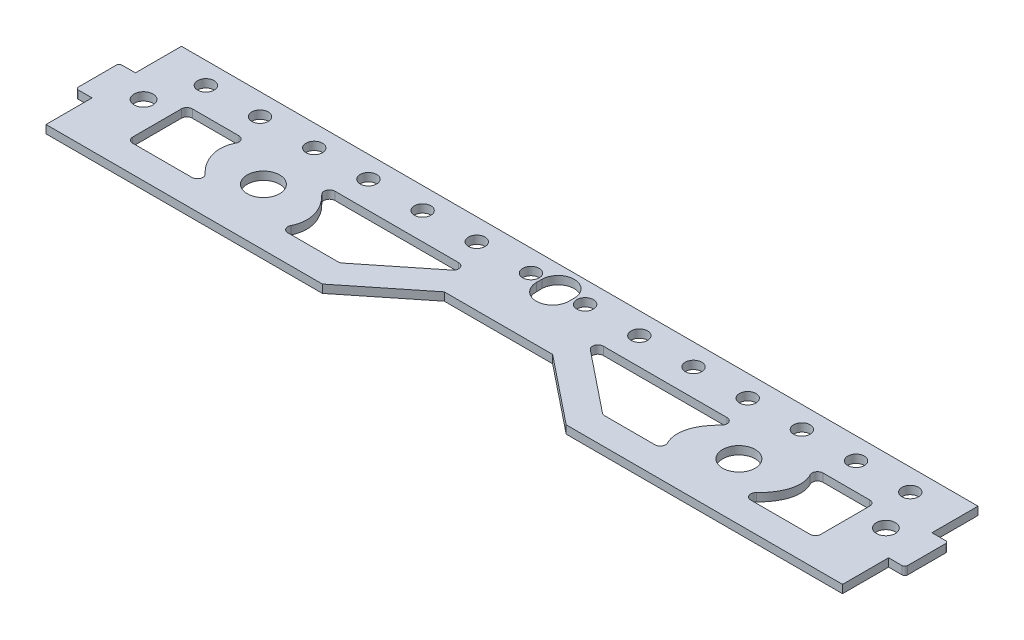
SolidWorks part; units mm, degrees
material "Thornel Mat VMA"
ref_plane "前视基准面" through (0, 0, 0) normal (0, 0, 1) x (1, 0, 0)
ref_plane "上视基准面" through (0, 0, 0) normal (0, 1, 0) x (1, 0, 0)
ref_plane "右视基准面" through (0, 0, 0) normal (1, 0, 0) x (0, 0, -1)
sketch "草图1" plane through (0, 0, 0) normal (0, 1, 0) x (1, 0, 0)
  line L1 (-73.5, 12.5) -> (73.5, 12.5)
  line L2 (-73.5, 12.5) -> (-73.5, -12.5)
  line L3 (-73.5, -12.5) -> (73.5, -12.5)
  line L4 (73.5, 12.5) -> (73.5, -12.5)
  line L5 (-73.5, 12.5) -> (73.5, -12.5) construction
  line L6 (-73.5, -12.5) -> (73.5, 12.5) construction
  point P0 (0, 0)
  dimension "D1" = 147
  dimension "D2" = 25
extrude "凸台-拉伸1" add sketch "草图1" along normal blind 1.5
sketch "草图2" plane through (0, 0, 0) normal (0, -1, 0) x (1, 0, 0)
  line L0 (10, 2.5) -> (-10, 2.5)
  line L1 (-10, 2.5) -> (-22.5, 12.5)
  line L2 (-73.5, 12.5) -> (73.5, 12.5) construction
  line L3 (-22.5, 12.5) -> (22.5, 12.5)
  line L4 (22.5, 12.5) -> (10, 2.5)
  point P5 (0, 2.5)
  point P7 (0, 12.5)
  dimension "D1" = 10
  dimension "D2" = 20
  dimension "D3" = 45
extrude "切除-拉伸1" cut sketch "草图2" against normal through all
sketch "草图4" plane through (0, 1.5, 0) normal (0, 1, 0) x (1, 0, 0)
  line L0 (73, 12.5) -> (-73, 12.5) construction
  line L1 (73.5, -12.5) -> (63.5, -12.5)
  line L2 (73.5, -12.5) -> (73.5, 12.5)
  line L3 (73.5, 12.5) -> (63.5, 12.5)
  line L4 (63.5, -12.5) -> (63.5, 12.5)
  line L5 (73.5, -12) -> (73.5, 12) construction
  dimension "D1" = 10
  dimension "D2" = 25
extrude "凸台-拉伸2" add sketch "草图4" against normal up to surface (1.5 mm away) up to face at (0, 0, 3.75)
mirror "镜向4" about plane through (0, 0, 0) normal (1, 0, 0) of "凸台-拉伸2"
sketch "草图5" plane through (0, 0, 0) normal (0, -1, 0) x (1, 0, 0)
  line L0 (73.5, -12.5) -> (-73.5, -12.5) construction
  line L1 (-73.5, -12.5) -> (-73.5, 12.5) construction
  line L2 (73.5, 12.5) -> (73.5, -12.5) construction
  circle A0 centre (-68.5, -0.5) radius 1.75
  circle A1 centre (68.5, -0.5) radius 1.75
  dimension "D2" = 5
  dimension "D4" = 5
  dimension "D5" = 3.5
  dimension "D1" = 12
  dimension "D3" = 12
extrude "切除-拉伸3" cut sketch "草图5" against normal through all
sketch "草图6" plane through (0, 1.5, 0) normal (0, 1, 0) x (1, 0, 0)
  line L0 (0, 8.5) -> (0, 7.5) construction
  line L1 (3, 8.5) -> (3, 7.5)
  line L2 (-3, 8.5) -> (-3, 7.5)
  arc A0 (3, 8.5) -> (-3, 8.5) centre (0, 8.5) ccw
  arc A1 (-3, 7.5) -> (3, 7.5) centre (0, 7.5) ccw
  point P3 (0, 8)
  dimension "D3" = 3
  dimension "D1" = 8
  dimension "D2" = 1
extrude "切除-拉伸4" cut sketch "草图6" against normal through all
sketch "草图7" plane through (0, 1.5, 0) normal (0, 1, 0) x (1, 0, 0)
  line L0 (-68.5, 0) -> (68.5, 0) construction
  line L1 (-73.5, 12.5) -> (-73.5, -12.5) construction
  line L2 (-76.5, -4) -> (-73.5, -4)
  line L3 (-76.5, -4) -> (-76.5, 4)
  line L4 (-76.5, 4) -> (-73.5, 4)
  line L5 (-73.5, -4) -> (-73.5, 4)
  line L6 (-76.5, -4) -> (-73.5, 4) construction
  line L7 (-76.5, 4) -> (-73.5, -4) construction
  line L8 (73.5, -12.5) -> (73.5, 12.5) construction
  line L9 (76.5, -4) -> (73.5, -4)
  line L10 (76.5, -4) -> (76.5, 4)
  line L11 (76.5, 4) -> (73.5, 4)
  line L12 (73.5, -4) -> (73.5, 4)
  line L13 (76.5, -4) -> (73.5, 4) construction
  line L14 (76.5, 4) -> (73.5, -4) construction
  point P1 (-75, 0)
  point P12 (75, 0)
  dimension "D1" = 8
  dimension "D2" = 3
extrude "凸台-拉伸3" add sketch "草图7" against normal up to surface (1.5 mm away) up to face at (0, 0, -8)
fillet "圆角4" radius 0.5 4 edges at (76.5, 0.75, 4) (76.5, 0.75, -4) (-76.5, 0.75, 4) (-76.5, 0.75, -4)
sketch "草图8" plane through (0, 0, 0) normal (0, -1, 0) x (1, 0, 0)
  line L0 (-65, -8.5) -> (-45, -8.5) construction
  line L2 (73.5, -12.5) -> (-73.5, -12.5) construction
  line L3 (0, 0) -> (0, -50000) construction
  circle A0 centre (-65, -8.5) radius 1.525
  circle A1 centre (-45, -8.5) radius 1.525
  circle A2 centre (-35, -8.5) radius 1.525
  circle A3 centre (-55, -8.5) radius 1.525
  circle A4 centre (-25, -8.5) radius 1.525
  circle A5 centre (-45, -8.5) radius 1.525
  circle A6 centre (-15, -8.5) radius 1.525
  circle A7 centre (-35, -8.5) radius 1.525
  circle A8 centre (-5, -8.5) radius 1.525
  circle A9 centre (-25, -8.5) radius 1.525
  circle A10 centre (5, -8.5) radius 1.525
  circle A11 centre (-15, -8.5) radius 1.525
  circle A12 centre (15, -8.5) radius 1.525
  circle A13 centre (-5, -8.5) radius 1.525
  circle A14 centre (25, -8.5) radius 1.525
  circle A15 centre (5, -8.5) radius 1.525
  circle A16 centre (35, -8.5) radius 1.525
  circle A17 centre (15, -8.5) radius 1.525
  circle A18 centre (45, -8.5) radius 1.525
  circle A19 centre (25, -8.5) radius 1.525
  circle A20 centre (55, -8.5) radius 1.525
  circle A21 centre (35, -8.5) radius 1.525
  circle A22 centre (65, -8.5) radius 1.525
  circle A23 centre (45, -8.5) radius 1.525
  dimension "D2" = 3.05
  dimension "D6" = 10
  dimension "D1" = 20
  dimension "D4" = 4
  dimension "D5" = 12
extrude "切除-拉伸5" cut sketch "草图8" against normal blind 10 contours A14 | A22 | A16 | A18 | A12 | A10 | A8 | A6 | A4 | A2 | A1 | A3 | A20 | A0
sketch "草图9" plane through (0, 0, 0) normal (0, -1, 0) x (1, 0, 0)
  line L0 (-63.5, 7.5) -> (-24.2539, 7.5)
  line L1 (-24.2539, 7.5) -> (-10.5039, -3.5)
  line L2 (-10.5039, -3.5) -> (-63.5, -3.5)
  line L3 (-63.5, -3.5) -> (-63.5, 7.5)
  line L4 (0, 0) -> (0, -50000) construction
  line L5 (-22.5, 12.5) -> (-10, 2.5) construction
  line L6 (-73.5, 12.5) -> (-22.5, 12.5) construction
  line L7 (-73.5, 4) -> (-73.5, 12.5) construction
  line L8 (-43.877, 2) -> (-43.877, 7.5) construction
  line L9 (-43.877, 2) -> (-63.5, 2) construction
  line L10 (-53.2739, -1.4202) -> (-43.877, 2) construction
  circle A0 centre (-55, -8.5) radius 1.525 construction
  circle A1 centre (-43.877, 2) radius 3
  ellipse E0 centre (-43.877, 2) end of major axis (-34.48, 5.4202) minor radius 7
  dimension "D5" = 7
  dimension "D6" = 6
  dimension "D1" = 10
  dimension "D2" = 5
  dimension "D3" = 5
  dimension "D4" = 5
  dimension "D7" = 10
  dimension "D8" = 160
extrude "切除-拉伸6" cut sketch "草图9" against normal blind 10
mirror "镜向5" about plane through (0, 0, 0) normal (1, 0, 0) of "切除-拉伸6"
fillet "圆角5" radius 1 16 edges at (39.1858, 0.75, -3.5) (51.8484, 0.75, -3.5) (10.5039, 0.75, -3.5) (24.2539, 0.75, 7.5) (35.9055, 0.75, 7.5) (48.5681, 0.75, 7.5) (-24.2539, 0.75, 7.5) (-10.5039, 0.75, -3.5) (-39.1858, 0.75, -3.5) (-51.8484, 0.75, -3.5) (-35.9055, 0.75, 7.5) (-48.5681, 0.75, 7.5) (-63.5, 0.75, -3.5) (63.5, 0.75, 7.5) (63.5, 0.75, -3.5) (-63.5, 0.75, 7.5)
